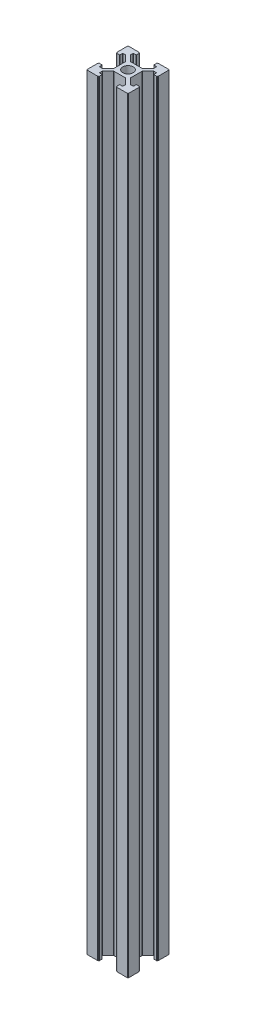
SolidWorks part; units mm, degrees
material "6063-O"
ref_plane "Ön Düzlem" through (0, 0, 0) normal (0, 0, 1) x (1, 0, 0)
ref_plane "Üst Düzlem" through (0, 0, 0) normal (0, 1, 0) x (1, 0, 0)
ref_plane "Sağ Düzlem" through (0, 0, 0) normal (1, 0, 0) x (0, 0, -1)
sketch "Sketch1" plane through (0, 0, 0) normal (0, 1, 0) x (1, 0, 0)
  line L0 (-10, 4.65) -> (-9.8, 4.65)
  line L1 (-9.8, -10) -> (-4.65, -10)
  line L2 (-10, -9.8) -> (-10, -4.65)
  line L3 (-9.8, 10) -> (-4.65, 10)
  line L4 (10, -9.8) -> (10, -4.65)
  line L5 (-10, -10) -> (10, 10) construction
  line L6 (-10, 10) -> (10, -10) construction
  line L7 (-9.8, 4.65) -> (-9.8, 4.4)
  line L8 (-9.6, 4.2) -> (-8.4, 4.2)
  line L9 (-4, 2.8172) -> (-4, -2.8172)
  line L10 (-8.2, 4.4) -> (-8.2, 5.45)
  line L11 (-8, 5.65) -> (-6.8328, 5.65)
  line L12 (-6.6914, 5.5914) -> (-4.0586, 2.9586)
  line L13 (-9.8, -4.65) -> (-10, -4.65)
  line L14 (-6.6914, -5.5914) -> (-4.0586, -2.9586)
  line L15 (-8, -5.65) -> (-6.8328, -5.65)
  line L16 (-8.2, -4.4) -> (-8.2, -5.45)
  line L17 (-9.6, -4.2) -> (-8.4, -4.2)
  line L18 (-9.8, -4.65) -> (-9.8, -4.4)
  line L19 (4.65, 10) -> (4.65, 9.8)
  line L20 (-10, 4.65) -> (-10, 9.8)
  line L21 (4.65, 9.8) -> (4.4, 9.8)
  line L22 (4.2, 9.6) -> (4.2, 8.4)
  line L23 (4.4, 8.2) -> (5.45, 8.2)
  line L24 (5.65, 8) -> (5.65, 6.8328)
  line L25 (5.5914, 6.6914) -> (2.9586, 4.0586)
  line L26 (2.8172, 4) -> (-2.8172, 4)
  line L27 (-5.5914, 6.6914) -> (-2.9586, 4.0586)
  line L28 (-5.65, 8) -> (-5.65, 6.8328)
  line L29 (-4.4, 8.2) -> (-5.45, 8.2)
  line L30 (-4.2, 9.6) -> (-4.2, 8.4)
  line L31 (-4.65, 9.8) -> (-4.4, 9.8)
  line L32 (-4.65, 9.8) -> (-4.65, 10)
  line L33 (10, -4.65) -> (9.8, -4.65)
  line L34 (9.8, -4.65) -> (9.8, -4.4)
  line L35 (9.6, -4.2) -> (8.4, -4.2)
  line L36 (8.2, -4.4) -> (8.2, -5.45)
  line L37 (8, -5.65) -> (6.8328, -5.65)
  line L38 (6.6914, -5.5914) -> (4.0586, -2.9586)
  line L39 (4, -2.8172) -> (4, 2.8172)
  line L40 (6.6914, 5.5914) -> (4.0586, 2.9586)
  line L41 (8, 5.65) -> (6.8328, 5.65)
  line L42 (8.2, 4.4) -> (8.2, 5.45)
  line L43 (9.6, 4.2) -> (8.4, 4.2)
  line L44 (9.8, 4.65) -> (9.8, 4.4)
  line L45 (9.8, 4.65) -> (10, 4.65)
  line L46 (-4.65, -10) -> (-4.65, -9.8)
  line L47 (-4.65, -9.8) -> (-4.4, -9.8)
  line L48 (-4.2, -9.6) -> (-4.2, -8.4)
  line L49 (-4.4, -8.2) -> (-5.45, -8.2)
  line L50 (-5.65, -8) -> (-5.65, -6.8328)
  line L51 (-5.5914, -6.6914) -> (-2.9586, -4.0586)
  line L52 (-2.8172, -4) -> (2.8172, -4)
  line L53 (5.5914, -6.6914) -> (2.9586, -4.0586)
  line L54 (5.65, -8) -> (5.65, -6.8328)
  line L55 (4.4, -8.2) -> (5.45, -8.2)
  line L56 (4.2, -9.6) -> (4.2, -8.4)
  line L57 (4.65, -9.8) -> (4.4, -9.8)
  line L58 (4.65, -9.8) -> (4.65, -10)
  line L59 (4.65, -10) -> (9.8, -10)
  line L60 (10, 4.65) -> (10, 9.8)
  line L61 (4.65, 10) -> (9.8, 10)
  arc A0 (-9.8, 4.4) -> (-9.6, 4.2) centre (-9.6, 4.4) ccw
  arc A1 (-9.8, -4.4) -> (-9.6, -4.2) centre (-9.6, -4.4) cw
  arc A2 (-8.4, 4.2) -> (-8.2, 4.4) centre (-8.4, 4.4) ccw
  arc A3 (-8.2, 5.45) -> (-8, 5.65) centre (-8, 5.45) cw
  arc A4 (-6.6914, 5.5914) -> (-6.8328, 5.65) centre (-6.8328, 5.45) ccw
  arc A5 (-4, 2.8172) -> (-4.0586, 2.9586) centre (-4.2, 2.8172) ccw
  arc A6 (-6.6914, -5.5914) -> (-6.8328, -5.65) centre (-6.8328, -5.45) cw
  arc A7 (-4, -2.8172) -> (-4.0586, -2.9586) centre (-4.2, -2.8172) cw
  arc A8 (-8, -5.65) -> (-8.2, -5.45) centre (-8, -5.45) cw
  arc A9 (-8.2, -4.4) -> (-8.4, -4.2) centre (-8.4, -4.4) ccw
  arc A10 (4.4, 9.8) -> (4.2, 9.6) centre (4.4, 9.6) ccw
  arc A11 (4.2, 8.4) -> (4.4, 8.2) centre (4.4, 8.4) ccw
  arc A12 (5.45, 8.2) -> (5.65, 8) centre (5.45, 8) cw
  arc A13 (5.5914, 6.6914) -> (5.65, 6.8328) centre (5.45, 6.8328) ccw
  arc A14 (2.8172, 4) -> (2.9586, 4.0586) centre (2.8172, 4.2) ccw
  arc A15 (-2.8172, 4) -> (-2.9586, 4.0586) centre (-2.8172, 4.2) cw
  arc A16 (-5.5914, 6.6914) -> (-5.65, 6.8328) centre (-5.45, 6.8328) cw
  arc A17 (-5.65, 8) -> (-5.45, 8.2) centre (-5.45, 8) cw
  arc A18 (-4.4, 8.2) -> (-4.2, 8.4) centre (-4.4, 8.4) ccw
  arc A19 (-4.4, 9.8) -> (-4.2, 9.6) centre (-4.4, 9.6) cw
  arc A20 (9.8, -4.4) -> (9.6, -4.2) centre (9.6, -4.4) ccw
  arc A21 (8.4, -4.2) -> (8.2, -4.4) centre (8.4, -4.4) ccw
  arc A22 (8.2, -5.45) -> (8, -5.65) centre (8, -5.45) cw
  arc A23 (6.6914, -5.5914) -> (6.8328, -5.65) centre (6.8328, -5.45) ccw
  arc A24 (4, -2.8172) -> (4.0586, -2.9586) centre (4.2, -2.8172) ccw
  arc A25 (4, 2.8172) -> (4.0586, 2.9586) centre (4.2, 2.8172) cw
  arc A26 (6.6914, 5.5914) -> (6.8328, 5.65) centre (6.8328, 5.45) cw
  arc A27 (8, 5.65) -> (8.2, 5.45) centre (8, 5.45) cw
  arc A28 (8.2, 4.4) -> (8.4, 4.2) centre (8.4, 4.4) ccw
  arc A29 (9.8, 4.4) -> (9.6, 4.2) centre (9.6, 4.4) cw
  arc A30 (-4.4, -9.8) -> (-4.2, -9.6) centre (-4.4, -9.6) ccw
  arc A31 (-4.2, -8.4) -> (-4.4, -8.2) centre (-4.4, -8.4) ccw
  arc A32 (-5.45, -8.2) -> (-5.65, -8) centre (-5.45, -8) cw
  arc A33 (-5.5914, -6.6914) -> (-5.65, -6.8328) centre (-5.45, -6.8328) ccw
  arc A34 (-2.8172, -4) -> (-2.9586, -4.0586) centre (-2.8172, -4.2) ccw
  arc A35 (2.8172, -4) -> (2.9586, -4.0586) centre (2.8172, -4.2) cw
  arc A36 (5.5914, -6.6914) -> (5.65, -6.8328) centre (5.45, -6.8328) cw
  arc A37 (5.65, -8) -> (5.45, -8.2) centre (5.45, -8) cw
  arc A38 (4.4, -8.2) -> (4.2, -8.4) centre (4.4, -8.4) ccw
  arc A39 (4.4, -9.8) -> (4.2, -9.6) centre (4.4, -9.6) cw
  arc A40 (-9.8, -10) -> (-10, -9.8) centre (-9.8, -9.8) cw
  arc A41 (9.8, -10) -> (10, -9.8) centre (9.8, -9.8) ccw
  arc A42 (10, 9.8) -> (9.8, 10) centre (9.8, 9.8) ccw
  arc A43 (-10, 9.8) -> (-9.8, 10) centre (-9.8, 9.8) cw
  circle A44 centre (0, 0) radius 2.5
  point P0 (0, 0)
  point P12 (-9.8, 4.2)
  point P27 (-9.8, -4.2)
  point P30 (-8.2, 4.2)
  point P33 (-8.2, 5.65)
  point P36 (-6.75, 5.65)
  point P39 (-4, 2.9)
  point P42 (-6.75, -5.65)
  point P45 (-4, -2.9)
  point P48 (-8.2, -5.65)
  point P51 (-8.2, -4.2)
  dimension "D11" = 0.2
  dimension "D13" = 0.2
  dimension "D14" = 5
  dimension "D1" = 20
  dimension "D2" = 20
  dimension "D3" = 5.35
  dimension "D4" = 0.2
  dimension "D5" = 0.45
  dimension "D6" = 1.6
  dimension "D7" = 4.2
  dimension "D8" = 1.45
  dimension "D9" = 1.45
  dimension "D10" = 135
  dimension "D12" = 4
extrude "Boss-Extrude1" add sketch "Sketch1" along normal blind 370
